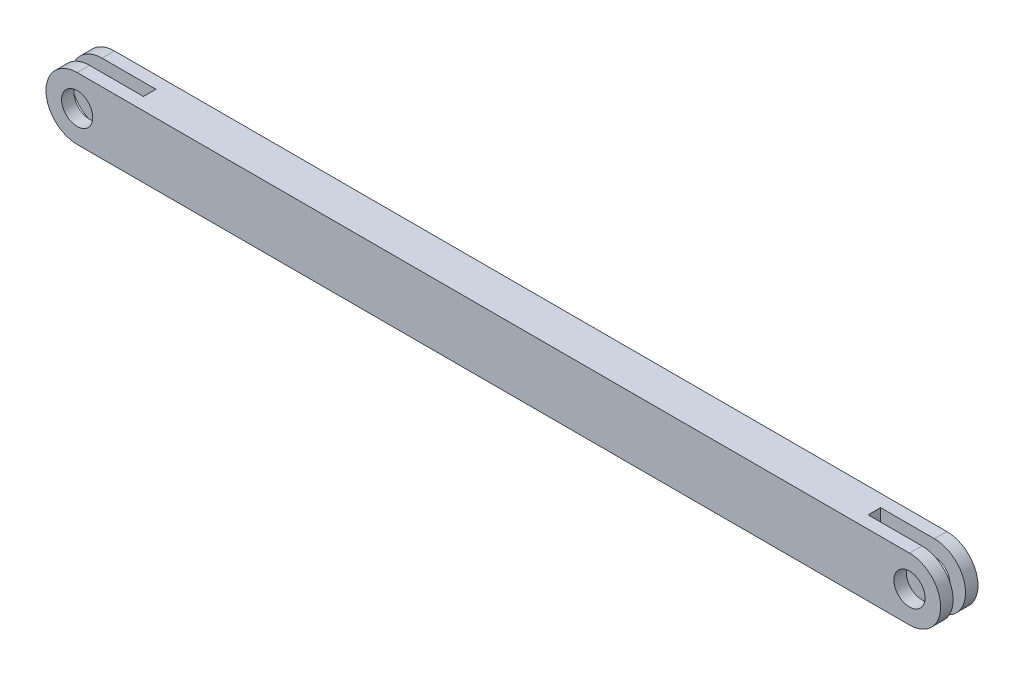
SolidWorks part; units mm, degrees
ref_plane "Спереди" through (0, 0, 0) normal (0, 0, 1) x (1, 0, 0)
ref_plane "Сверху" through (0, 0, 0) normal (0, 1, 0) x (1, 0, 0)
ref_plane "Справа" through (0, 0, 0) normal (1, 0, 0) x (0, 0, -1)
other "Configuration Table"
sketch "Sketch19" plane through (0, 0, 0) normal (0, 0, 1) x (1, 0, 0)
  line L0 (0, -5) -> (0, 5) construction
  line L1 (56.8219, -5.3508) -> (-58.1781, -5.3508)
  line L2 (56.8219, -5.3508) -> (56.8219, 4.6492)
  line L3 (56.8219, 4.6492) -> (-58.1781, 4.6492)
  line L4 (-58.1781, -5.3508) -> (-58.1781, 4.6492)
  line L5 (56.8219, -5.3508) -> (-58.1781, 4.6492) construction
  line L6 (56.8219, 4.6492) -> (-58.1781, -5.3508) construction
  point P0 (-0.6781, -0.3508)
  point P6 (-0.6781, -5.3508)
  point P8 (-0.6781, 4.6492)
  dimension "D1" = 115
  dimension "D2" = 10
extrude "Boss-Extrude4" add sketch "Sketch19" along normal mid plane 6 contours L3 L4 L1 L2
sketch3d "3DSketch5" plane through (0, 0, 0) normal (0, 0, 1) x (1, 0, 0)
sketch "Sketch21" plane through (0, 0, 3) normal (0, 0, 1) x (1, 0, 0)
  line L0 (56.8219, 4.6492) -> (66.8219, 4.6492)
  line L2 (56.8219, -5.3508) -> (66.8219, -5.3508)
  line L3 (56.8219, 4.6492) -> (56.8219, -5.3508)
  arc A0 (66.8219, 4.6492) -> (66.8219, -5.3508) centre (66.8219, -0.3508) cw
  circle A1 centre (66.8219, -0.3508) radius 2.5
  line M1 (56.8219, -5.3508) -> (56.8219, 4.6492)
  dimension "D1" = 10
  dimension "D2" = 5
extrude "Boss-Extrude13" add sketch "Sketch21" against normal blind 2 contours A0 L0 L2 A1 M1
mirror "Mirror14" about plane through (0, 0, 0) normal (0, 0, 1) of "Boss-Extrude4", "Boss-Extrude13"
sketch3d "3DSketch8"
  line L0 (0, -5, 0) -> (0, 5, 0) construction
ref_plane "Plane12" through (0, 0, 0) normal (1, 0, 0) x (0, 0, -1)
mirror "Mirror15" about plane through (0, 0, 0) normal (1, 0, 0) of "Boss-Extrude4", "Boss-Extrude13", "Mirror14"
